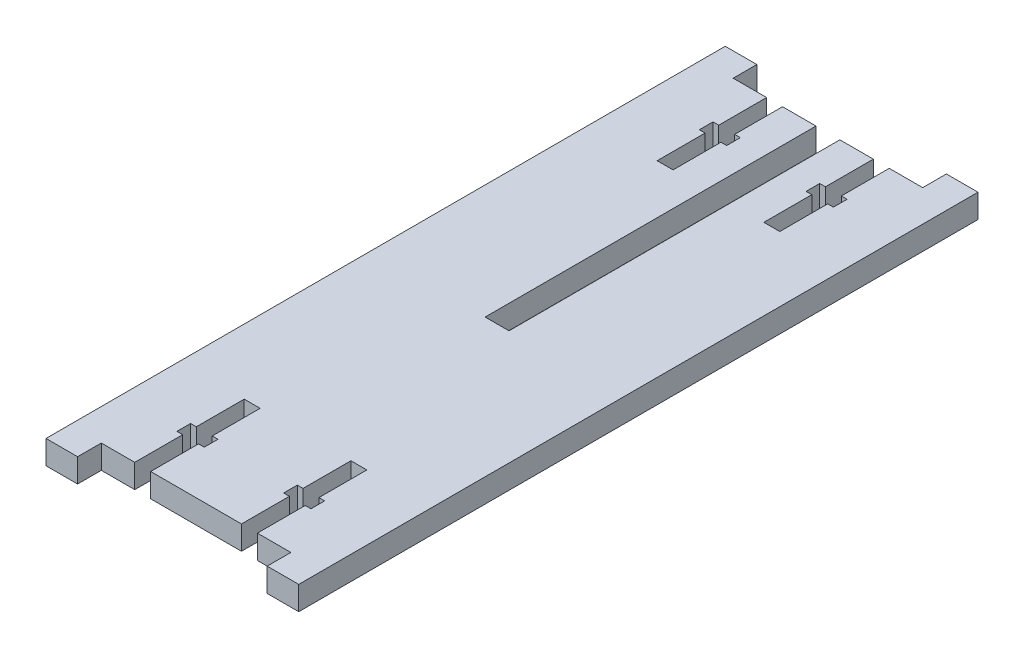
SolidWorks part; units mm, degrees
ref_plane "Front Plane" through (0, 0, 0) normal (0, 0, 1) x (1, 0, 0)
ref_plane "Top Plane" through (0, 0, 0) normal (0, 1, 0) x (1, 0, 0)
ref_plane "Right Plane" through (0, 0, 0) normal (1, 0, 0) x (0, 0, -1)
sketch "Sketch1" plane through (0, 0, 0) normal (0, 1, 0) x (1, 0, 0)
  line L0 (-2.4, 63.5) -> (-2.4, -3)
  line L1 (19.05, -63.5) -> (-19.05, -63.5)
  line L2 (25.4, -63.5) -> (25.4, 63.5)
  line L3 (19.05, 63.5) -> (2.4, 63.5)
  line L4 (-25.4, -63.5) -> (-25.4, 63.5)
  line L5 (25.4, -63.5) -> (-25.4, 63.5) construction
  line L6 (25.4, 63.5) -> (-25.4, -63.5) construction
  line L7 (-2.4, -3) -> (2.4, -3)
  line L8 (2.4, -3) -> (2.4, 63.5)
  line L9 (25.4, 0) -> (-25.4, 0) construction
  line L10 (0, -63.5) -> (0, 63.5) construction
  line L11 (-25.4, 63.5) -> (-25.4, 68.2625)
  line L12 (-25.4, 68.2625) -> (-19.05, 68.2625)
  line L13 (-19.05, 68.2625) -> (-19.05, 63.5)
  line L14 (-2.4, 63.5) -> (-19.05, 63.5)
  line L15 (-2.4, 63.5) -> (-6.2249, 63.5)
  line L16 (-25.4, 63.5) -> (-19.05, 63.5) construction
  line L17 (25.4, 68.2625) -> (19.05, 68.2625)
  line L18 (19.05, 68.2625) -> (19.05, 63.5)
  line L19 (25.4, 63.5) -> (25.4, 68.2625)
  line L20 (25.4, -63.5) -> (25.4, -68.2625)
  line L21 (25.4, -68.2625) -> (19.05, -68.2625)
  line L22 (19.05, -68.2625) -> (19.05, -63.5)
  line L23 (-19.05, -68.2625) -> (-19.05, -63.5)
  line L24 (-25.4, -68.2625) -> (-19.05, -68.2625)
  line L25 (-25.4, -63.5) -> (-25.4, -68.2625)
  point P0 (0, 0)
  point P10 (2.4435, -1.9051)
  point P14 (0, 0)
  point P17 (0, 0)
  point P30 (-13.3651, 63.5)
  point P31 (-1.5967, 63.5)
  point P32 (0, 0)
  point P33 (0, 0)
  point P34 (2.4, 0)
  point P35 (-6.2249, 63.5)
  point P36 (1.8659, 63.5)
  point P37 (0, -3)
  dimension "D1" = 127
  dimension "D2" = 50.8
  dimension "D3" = 4.8
  dimension "D4" = 4.7625
  dimension "D5" = 6.35
  dimension "D6" = 3
extrude "Boss-Extrude1" add sketch "Sketch1" along normal blind 4.7625 contours L4 L25 L24 L23 L1 L22 L21 L20 L2 L19 L17 L18 L3 L8 L7 L0 L14 L13 L12 L11
sketch "Sketch2" plane through (0, 4.7625, 0) normal (0, 1, 0) x (1, 0, 0)
  line L0 (-2.4, 63.5) -> (-19.05, 63.5) construction
  line L1 (-12.325, 63.5) -> (-9.125, 63.5)
  line L2 (-12.325, 63.5) -> (-12.325, 41.5)
  line L3 (-12.325, 41.5) -> (-9.125, 41.5)
  line L4 (-9.125, 63.5) -> (-9.125, 41.5)
  line L5 (-19.05, 63.5) -> (-2.4, 63.5) construction
  line L6 (25.4, 0) -> (-25.4, 0) construction
  line L8 (25.4, 0) -> (-25.4, 0) construction
  line L9 (0, -63.5) -> (0, 63.5) construction
  line L10 (0, -63.5) -> (0, 63.5) construction
  line L11 (25.4, -63.5) -> (25.4, 63.5) construction
  line L12 (19.05, 63.5) -> (2.4, 63.5) construction
  line L13 (12.325, 41.5) -> (9.125, 41.5)
  line L14 (9.125, 63.5) -> (9.125, 41.5)
  line L15 (12.325, 63.5) -> (9.125, 63.5)
  line L16 (12.325, 63.5) -> (12.325, 41.5)
  line L17 (12.325, -63.5) -> (12.325, -41.5)
  line L18 (12.325, -63.5) -> (9.125, -63.5)
  line L19 (9.125, -63.5) -> (9.125, -41.5)
  line L20 (12.325, -41.5) -> (9.125, -41.5)
  line L21 (-12.325, -41.5) -> (-9.125, -41.5)
  line L22 (-9.125, -63.5) -> (-9.125, -41.5)
  line L23 (-12.325, -63.5) -> (-9.125, -63.5)
  line L24 (-12.325, -63.5) -> (-12.325, -41.5)
  line L25 (13.475, 51.125) -> (7.975, 51.125)
  line L26 (-13.475, 53.875) -> (-7.975, 53.875)
  line L27 (-13.475, 53.875) -> (-13.475, 51.125)
  line L28 (-13.475, 51.125) -> (-7.975, 51.125)
  line L29 (-7.975, 53.875) -> (-7.975, 51.125)
  line L30 (7.975, 53.875) -> (7.975, 51.125)
  line L31 (13.475, 53.875) -> (7.975, 53.875)
  line L32 (13.475, 53.875) -> (13.475, 51.125)
  line L33 (-13.475, -51.125) -> (-7.975, -51.125)
  line L34 (-7.975, -53.875) -> (-7.975, -51.125)
  line L35 (-13.475, -53.875) -> (-7.975, -53.875)
  line L36 (-13.475, -53.875) -> (-13.475, -51.125)
  line L37 (13.475, -53.875) -> (13.475, -51.125)
  line L38 (13.475, -53.875) -> (7.975, -53.875)
  line L39 (7.975, -53.875) -> (7.975, -51.125)
  line L40 (13.475, -51.125) -> (7.975, -51.125)
  point P9 (-10.725, 51.125)
  point P13 (-10.725, 63.5)
  point P14 (-10.725, 41.5)
  point P19 (0, 0)
  point P24 (0, 0)
  point P27 (-12.325, 52.5)
  point P46 (-13.475, 52.5)
  line M14 (-19.05, -63.5) -> (19.05, -63.5)
  line M20 (19.05, 63.5) -> (2.4, 63.5)
  line M24 (-2.4, 63.5) -> (-19.05, 63.5)
  dimension "D1" = 22
  dimension "D2" = 3.2
  dimension "D3" = 5.5
  dimension "D4" = 2.75
extrude "Cut-Extrude1" cut sketch "Sketch2" against normal up to surface (4.7625 mm away) contours L2 L26 L4 M24 | L2 L28 L4 L26 | L29 L26 L4 L28 | L28 L2 L3 L4 | L27 L28 L2 L26 | L31 L16 L14 M20 | L16 L31 L14 L25 | L14 L31 L30 L25 | L32 L31 L16 L25 | L16 L25 L14 L13 | L24 L33 L22 L21 | L35 L24 L22 M14 | L36 L35 L24 L33 | L24 L35 L22 L33 | L22 L35 L34 L33 | L40 L17 L20 L19 | L19 L40 L39 L38 | L17 L40 L19 L38 | L37 L40 L17 L38 | L17 L38 L19 M14 up to face at (0, 0, -7.5625)
